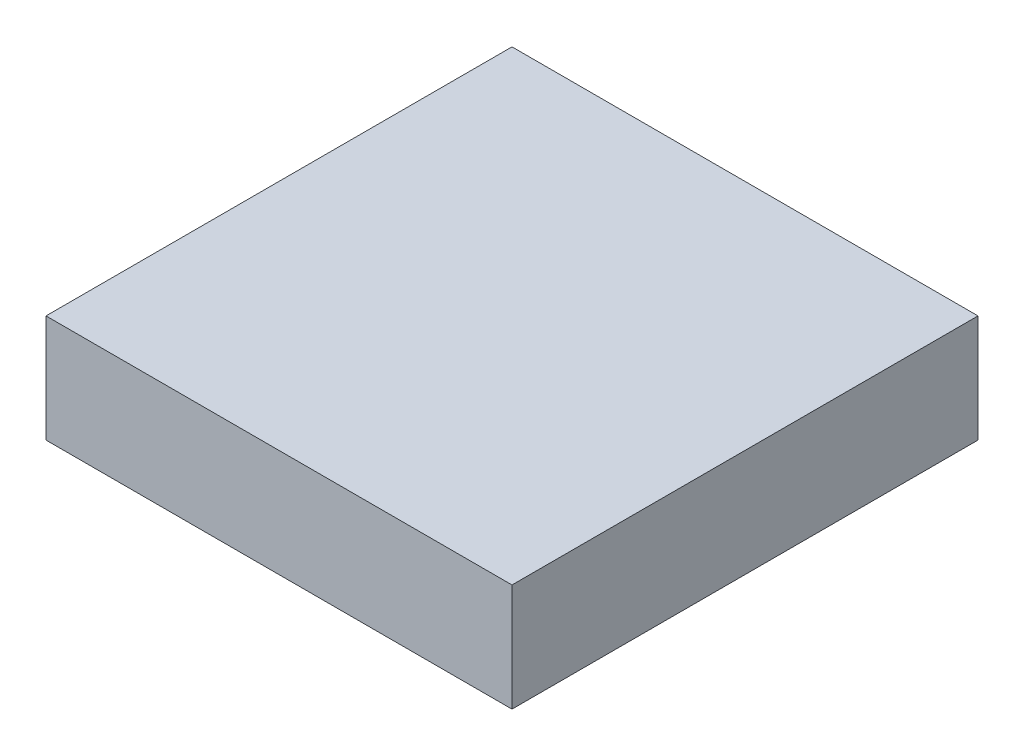
SolidWorks part; units mm, degrees
ref_plane "Front Plane" through (0, 0, 0) normal (0, 0, 1) x (1, 0, 0)
ref_plane "Top Plane" through (0, 0, 0) normal (0, 1, 0) x (1, 0, 0)
ref_plane "Right Plane" through (0, 0, 0) normal (1, 0, 0) x (0, 0, -1)
sketch "Sketch1" plane through (0, 0, 0) normal (0, 1, 0) x (1, 0, 0)
  line L1 (0, 0) -> (120, 0)
  line L2 (0, 0) -> (0, 120)
  line L3 (0, 120) -> (120, 120)
  line L4 (120, 0) -> (120, 120)
  dimension "D1" = 120
  dimension "D2" = 120
extrude "Boss-Extrude1" add sketch "Sketch1" along normal blind 27.7
